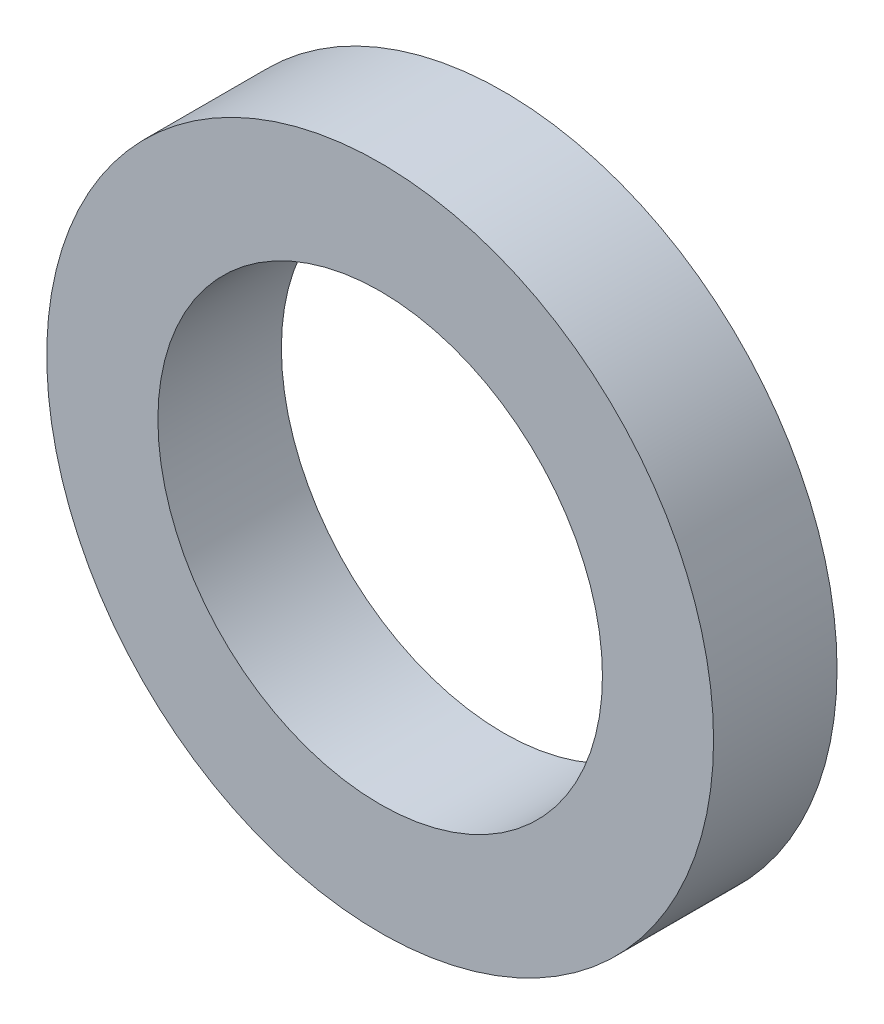
SolidWorks part; units mm, degrees
ref_plane "前视基准面" through (0, 0, 0) normal (0, 0, 1) x (1, 0, 0)
ref_plane "上视基准面" through (0, 0, 0) normal (0, 1, 0) x (1, 0, 0)
ref_plane "右视基准面" through (0, 0, 0) normal (1, 0, 0) x (0, 0, -1)
sketch "草图1" plane through (0, 0, 0) normal (0, 0, 1) x (1, 0, 0)
  circle A0 centre (0, 0) radius 2.7
  circle A1 centre (0, 0) radius 1.8
  dimension "D1" = 3.6
  dimension "D2" = 5.4
extrude "凸台-拉伸1" add sketch "草图1" along normal blind 1
